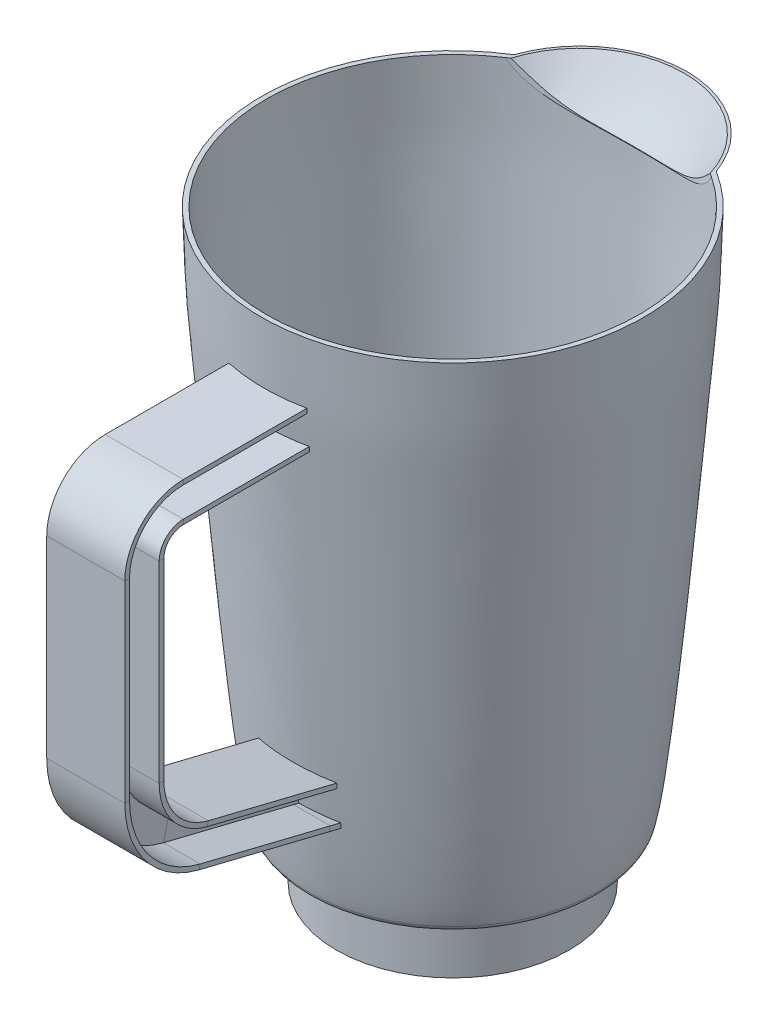
SolidWorks part; units mm, degrees
ref_plane "Front Plane" through (0, 0, 0) normal (0, 0, 1) x (1, 0, 0)
ref_plane "Top Plane" through (0, 0, 0) normal (0, 1, 0) x (1, 0, 0)
ref_plane "Right Plane" through (0, 0, 0) normal (1, 0, 0) x (0, 0, -1)
sketch "Sketch1" plane through (0, 0, 0) normal (1, 0, 0) x (0, 0, -1)
  line L0 (0, 190.5) -> (0, -63.121) construction
  line L1 (0, 0) -> (37.8587, 0) construction
  line L2 (37.8587, 0) -> (31.5087, 0)
  line L3 (31.5087, 0) -> (31.5087, 1.524)
  line L4 (31.5087, 1.524) -> (36.3347, 1.524)
  line L5 (36.3347, 1.524) -> (36.3347, 20.574)
  line L6 (36.3347, 20.574) -> (44.3443, 20.574)
  line L7 (37.8587, 0) -> (37.8587, 19.05)
  line L8 (37.8587, 19.05) -> (44.5393, 19.05)
  line L9 (0, 190.5) -> (60.7019, 190.5) construction
  line L10 (60.7019, 190.5) -> (62.2259, 190.5)
  line L11 (58.8774, 137.2765) -> (57.3534, 137.2765) construction
  arc A0 (44.3443, 20.574) -> (46.8419, 22.6515) centre (44.3443, 23.114) ccw
  arc A1 (47.0012, 20.965) -> (44.5393, 19.05) centre (44.5393, 21.59) cw
  spline S0 degree 3 poles (60.7019, 190.5) (59.6048, 162.6598) (60.5346, 179.1936) (49.4307, 36.6314) (46.8419, 22.6515) knots 0 0 0 0 0.492125 0.952522 0.952522 0.952522 0.952522
  spline S1 degree 3 poles (62.2259, 190.5) (61.2279, 162.6599) (62.2773, 180.1864) (50.4351, 34.4926) (47.0012, 20.965) knots 0 0 0 0 0.493367 0.955966 0.955966 0.955966 0.955966
  dimension "D11" = 2.54
  dimension "D10" = 2.54
  dimension "D1" = 37.8587
  dimension "D2" = 60.7019
  dimension "D3" = 1.524
  dimension "D4" = 1.524
  dimension "D5" = 6.35
  dimension "D6" = 19.05
  dimension "D7" = 1.524
  dimension "D8" = 1.524
  dimension "D9" = 190.5
  dimension "D12" = 1.524
revolve "Revolve1" add sketch "Sketch1" angle 360 about L0
sketch "Sketch2" plane through (0, 190.5, 0) normal (0, 1, 0) x (1, 0, 0)
  line L0 (0, -62.2259) -> (0, 62.2259)
  line L1 (0, 0) -> (0, 41.402)
  circle A0 centre (0, 0) radius 62.2259
  point P5 (0, 0)
  dimension "D1" = 124.4519
  dimension "D2" = 41.402
ref_plane "Plane1" through (0, 190.5, 62.2259) normal (0, 0, -1) x (-1, 0, 0)
sketch "Sketch3" plane through (0, 190.5, 62.2259) normal (0, 0, -1) x (-1, 0, 0)
  line L0 (0, 0) -> (0, -20.32) construction
  line L1 (12.7, -20.32) -> (-12.7, -20.32)
  line L2 (-12.7, -20.32) -> (-12.7, -21.844)
  line L3 (-12.7, -21.844) -> (-0.762, -21.844)
  line L4 (-0.762, -21.844) -> (-0.762, -31.496)
  line L5 (-0.762, -31.496) -> (-12.7, -31.496)
  line L6 (-12.7, -31.496) -> (-12.7, -33.02)
  line L7 (-12.7, -33.02) -> (12.7, -33.02)
  line L8 (0, -33.02) -> (0, -20.32)
  line L9 (0.762, -21.844) -> (0.762, -31.496)
  line L10 (12.7, -31.496) -> (12.7, -33.02)
  line L11 (0.762, -31.496) -> (12.7, -31.496)
  line L12 (12.7, -21.844) -> (0.762, -21.844)
  line L13 (12.7, -20.32) -> (12.7, -21.844)
  point P16 (0, -26.67)
  dimension "D1" = 20.32
  dimension "D2" = 12.7
  dimension "D3" = 12.7
  dimension "D4" = 1.524
  dimension "D5" = 0.762
ref_plane "Plane2" through (0, 0, 0) normal (1, 0, 0) x (0, 0, -1)
sketch "Sketch4" plane through (0, 0, 0) normal (1, 0, 0) x (0, 0, -1)
  line L0 (-62.2259, 163.83) -> (-100.3259, 163.83)
  line L1 (-113.0259, 151.13) -> (-113.0259, 88.4854)
  line L2 (-93.6976, 63.8218) -> (-51.3668, 53.401)
  line L3 (-51.3668, 53.401) -> (-22.0784, 46.1908)
  line L4 (-62.2259, 163.83) -> (-52.9657, 163.83)
  arc A0 (-113.0259, 151.13) -> (-100.3259, 163.83) centre (-100.3259, 151.13) cw
  arc A1 (-93.6976, 63.8218) -> (-113.0259, 88.4854) centre (-87.6259, 88.4854) cw
  spline S0 degree 3 poles (-62.2259, 190.5) (-61.2279, 162.6599) (-62.2773, 180.1864) (-50.4351, 34.4926) (-47.0012, 20.965) knots 0 0 0 0 0.493367 0.955966 0.955966 0.955966 0.955966 construction
  point P9 (-113.0259, 163.83)
  point P12 (-113.0259, 68.58)
  dimension "D4" = 12.7
  dimension "D5" = 25.4
  dimension "D1" = 50.8
  dimension "D2" = 95.25
  dimension "D3" = 63.5
sweep "Sweep4" add profiles "Sketch3" path "Sketch4"
sketch "Sketch11" plane through (0, 0, 0) normal (1, 0, 0) x (0, 0, -1)
  line L0 (74.6719, 190.5) -> (41.3979, 190.5) construction
  line L1 (-62.2259, 190.5) -> (62.2259, 190.5) construction
  line L2 (60.7019, 190.5) -> (60.7019, 179.07)
  line L3 (41.3979, 190.5) -> (41.3979, 175.5355)
  line L4 (74.6719, 190.5) -> (41.3979, 190.5)
  line L5 (74.6719, 190.5) -> (76.1959, 190.5)
  line L6 (41.3979, 175.5355) -> (41.3979, 174.0115)
  spline S0 degree 3 poles (46.8419, 22.6515) (49.4307, 36.6314) (60.5346, 179.1936) (59.6048, 162.6598) (60.7019, 190.5) knots 0 0 0 0 0.460398 0.952522 0.952522 0.952522 0.952522 construction
  spline S1 degree 3 poles (74.6719, 190.5) (69.793, 182.1189) (60.6123, 178.8621) (50.4294, 176.0064) (41.3979, 175.5355) knots 0 0 0 0 0.482414 1 1 1 1
  spline S2 degree 3 poles (76.1959, 190.5) (71.971, 182.3715) (60.4252, 176.6966) (50.5988, 174.6403) (41.3979, 174.0115) knots 0 0 0 0 0.507168 1 1 1 1
  point P6 (60.7019, 190.5)
  dimension "D1" = 33.274
  dimension "D2" = 13.97
  dimension "D3" = 11.43
  dimension "D4" = 1.524
  dimension "D5" = 1.524
  dimension "D6" = 1.524
revolve "Revolve2" add sketch "Sketch11" angle 360 about L3
ref_plane "Plane3" through (0, 190.5, -41.402) normal (0, 0, -1) x (-1, 0, 0)
sketch "Sketch13" plane through (0, 190.5, -41.402) normal (0, 0, -1) x (-1, 0, 0)
  line L0 (0, 0) -> (0, -15.24)
  line L1 (0, 0) -> (33.9162, 0)
  spline S0 degree 3 poles (0, -15.24) (21.8666, -14.9034) (25.2032, -11.1948) (33.9162, 0) knots 0 0 0 0 1 1 1 1
  dimension "D1" = 15.24
revolve "Cut-Revolve1" cut sketch "Sketch13" angle 360 about L0
ref_plane "Plane4" through (0, 23.114, 0) normal (0, 1, 0) x (1, 0, 0)
sketch "Sketch15" plane through (0, 23.114, 0) normal (0, 1, 0) x (1, 0, 0)
  circle A0 centre (0, 0) radius 46.7411
sketch "Sketch16" plane through (0, 190.5, 0) normal (0, 1, 0) x (1, 0, 0)
  circle A0 centre (0, 0) radius 60.7019
loft "Cut-Loft1" cut profiles "Sketch16", "Sketch15"
